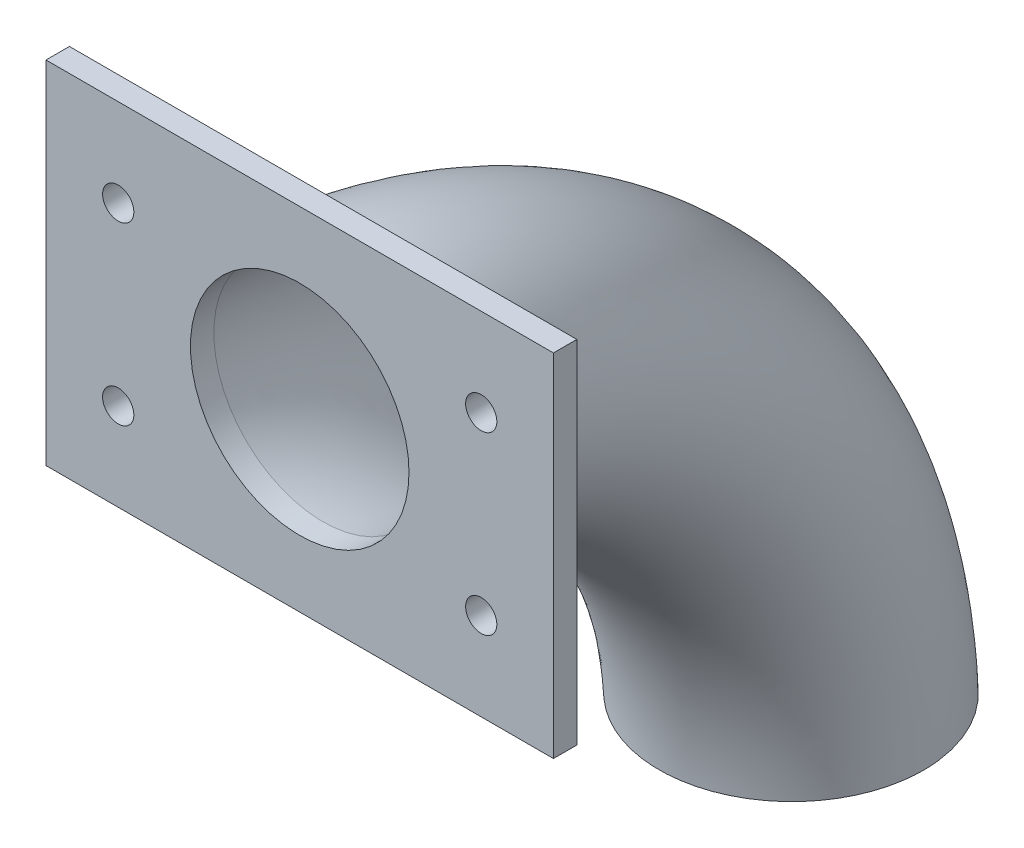
SolidWorks part; units mm, degrees
ref_plane "Plan de face" through (0, 0, 0) normal (0, 0, 1) x (1, 0, 0)
ref_plane "Plan de dessus" through (0, 0, 0) normal (0, 1, 0) x (1, 0, 0)
ref_plane "Plan de droite" through (0, 0, 0) normal (1, 0, 0) x (0, 0, -1)
sketch "Esquisse1" plane through (0, 0, 0) normal (0, 0, 1) x (1, 0, 0)
  circle A0 centre (0, 0) radius 14
  circle A1 centre (0, 0) radius 17
  dimension "D1" = 28
  dimension "D2" = 3
sketch "Esquisse2" plane through (0, 0, 0) normal (1, 0, 0) x (0, 0, -1)
  line L0 (0, 0) -> (0, -65) construction
  line L1 (0, -65) -> (60, -65) construction
  arc A0 (0, 0) -> (60, -65) centre (-6.9244, -66.5841) cw
  dimension "D1" = 65
  dimension "D2" = 60
sweep "Balayage1" add profiles "Esquisse1" path "Esquisse2"
sketch "Esquisse3" plane through (0, 0, 0) normal (0, 0, 1) x (1, 0, 0)
  line L0 (-32.5, 0) -> (-14, 0) construction
  line L1 (-32.5, 22.5) -> (32.5, 22.5)
  line L2 (-32.5, 22.5) -> (-32.5, -22.5)
  line L3 (-32.5, -22.5) -> (32.5, -22.5)
  line L4 (32.5, 22.5) -> (32.5, -22.5)
  line L5 (-32.5, 22.5) -> (32.5, -22.5) construction
  line L6 (-32.5, -22.5) -> (32.5, 22.5) construction
  line L7 (0, 22.5) -> (0, -22.5) construction
  line L8 (-23.25, 0) -> (-23.25, 22.5) construction
  circle A0 centre (0, 0) radius 14
  circle A1 centre (-23.25, 11.25) radius 2
  circle A2 centre (-23.25, -11.25) radius 2
  circle A3 centre (23.25, -11.25) radius 2
  circle A4 centre (23.25, 11.25) radius 2
  point P0 (0, 0)
  dimension "D3" = 4
  dimension "D4" = 9.25
  dimension "D1" = 65
  dimension "D2" = 45
extrude "Boss.-Extru.1" add sketch "Esquisse3" along normal blind 3
ref_plane "Plan1" through (0, -63, 0) normal (0, 1, 0) x (1, 0, 0)
sketch "Esquisse4" plane through (0, -63, 0) normal (0, 1, 0) x (1, 0, 0)
  line L1 (-28.2158, 78.2039) -> (28.2158, 78.2039)
  line L2 (-28.2158, 78.2039) -> (-28.2158, 41.8745)
  line L3 (-28.2158, 41.8745) -> (28.2158, 41.8745)
  line L4 (28.2158, 78.2039) -> (28.2158, 41.8745)
  line L5 (-28.2158, 78.2039) -> (28.2158, 41.8745) construction
  line L6 (-28.2158, 41.8745) -> (28.2158, 78.2039) construction
  point P0 (0, 60.0392)
extrude "Enlèv. mat.-Extru.1" cut sketch "Esquisse4" against normal blind 10
